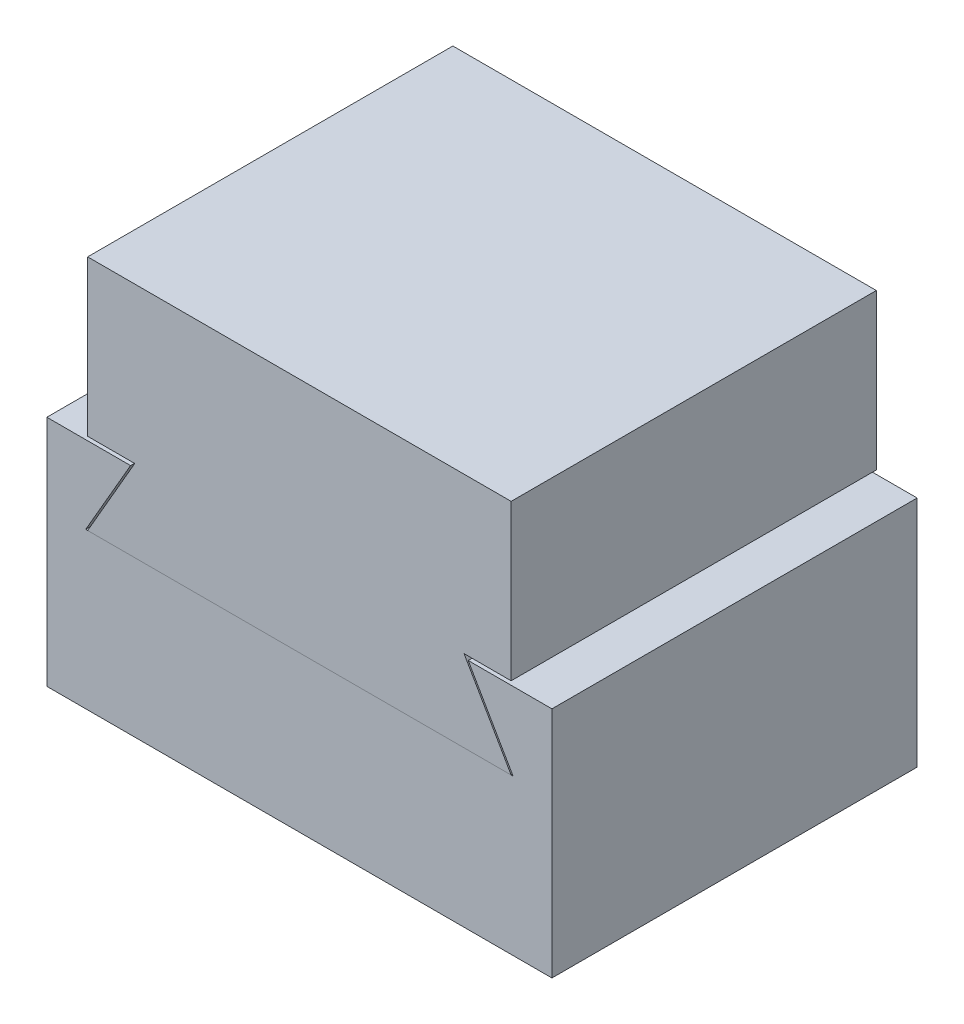
SolidWorks part; units mm, degrees
ref_plane "Front" through (0, 0, 0) normal (0, 0, 1) x (1, 0, 0)
ref_plane "Top" through (0, 0, 0) normal (0, 1, 0) x (1, 0, 0)
ref_plane "Right" through (0, 0, 0) normal (1, 0, 0) x (0, 0, -1)
sketch "Sketch1" plane through (0, 0, 0) normal (0, 0, 1) x (1, 0, 0)
  line L0 (-6.9215, 0) -> (6.9215, 0)
  line L1 (6.9215, 0) -> (5.3817, 2.667)
  line L2 (5.3817, 2.667) -> (6.9215, 2.667)
  line L3 (-6.9215, 0) -> (-5.3817, 2.667)
  line L4 (-5.3817, 2.667) -> (-6.9215, 2.667)
  line L5 (-6.9215, 2.667) -> (-6.9215, 7.747)
  line L6 (-6.9215, 7.747) -> (6.9215, 7.747)
  line L7 (6.9215, 7.747) -> (6.9215, 2.667)
  dimension "D1" = 13.843
  dimension "D2" = 60
  dimension "D3" = 60
  dimension "D4" = 2.667
extrude "Extrude1" add sketch "Sketch1" along normal blind 11.938
sketch "Sketch2" plane through (0, 0, 0) normal (0, 0, 1) x (1, 0, 0)
  line L0 (-6.985, 0) -> (6.985, 0)
  line L1 (6.985, 0) -> (5.5185, 2.54)
  line L2 (6.9215, 0) -> (5.3817, 2.667) construction
  line L3 (-6.985, 0) -> (-5.5185, 2.54)
  line L4 (-5.3817, 2.667) -> (-6.9215, 0) construction
  line L5 (5.5185, 2.54) -> (8.255, 2.54)
  line L6 (8.255, 2.54) -> (8.255, -5.08)
  line L7 (8.255, -5.08) -> (-8.255, -5.08)
  line L8 (-8.255, -5.08) -> (-8.255, 2.54)
  line L9 (-8.255, 2.54) -> (-5.5185, 2.54)
  dimension "D1" = 13.97
  dimension "D3" = 2.54
extrude "Extrude2" add sketch "Sketch2" along normal blind 11.938 separate body
